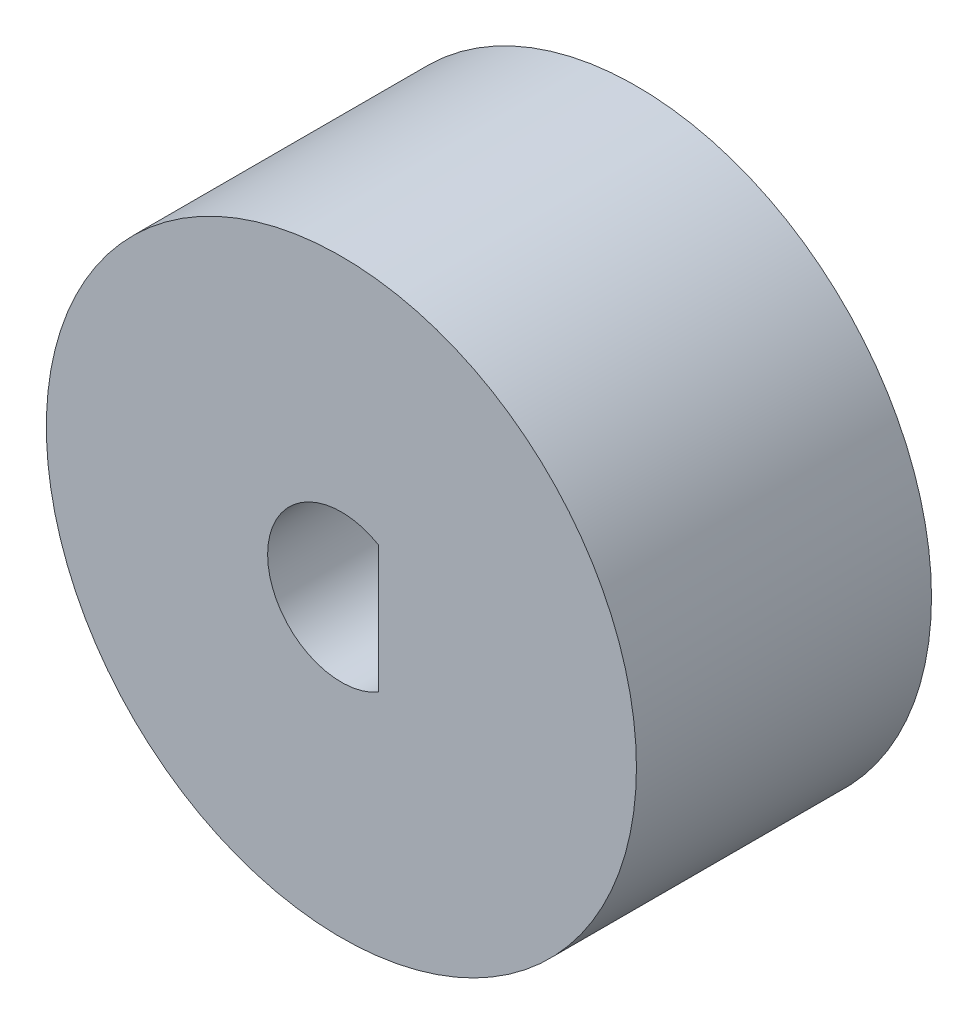
SolidWorks part; units mm, degrees
ref_plane "Front Plane" through (0, 0, 0) normal (0, 0, 1) x (1, 0, 0)
ref_plane "Top Plane" through (0, 0, 0) normal (0, 1, 0) x (1, 0, 0)
ref_plane "Right Plane" through (0, 0, 0) normal (1, 0, 0) x (0, 0, -1)
sketch "Sketch1" plane through (0, 0, 0) normal (0, 0, 1) x (1, 0, 0)
  line L0 (6.35, 10.9985) -> (6.35, -10.9985)
  circle A0 centre (0, 0) radius 50.8
  circle A1 centre (0, 0) radius 12.7
  dimension "D1" = 101.6
  dimension "D2" = 25.4
  dimension "D3" = 19.05
extrude "Boss-Extrude1" add sketch "Sketch1" along normal blind 50.8 contours A0 A1 | L0 A1
